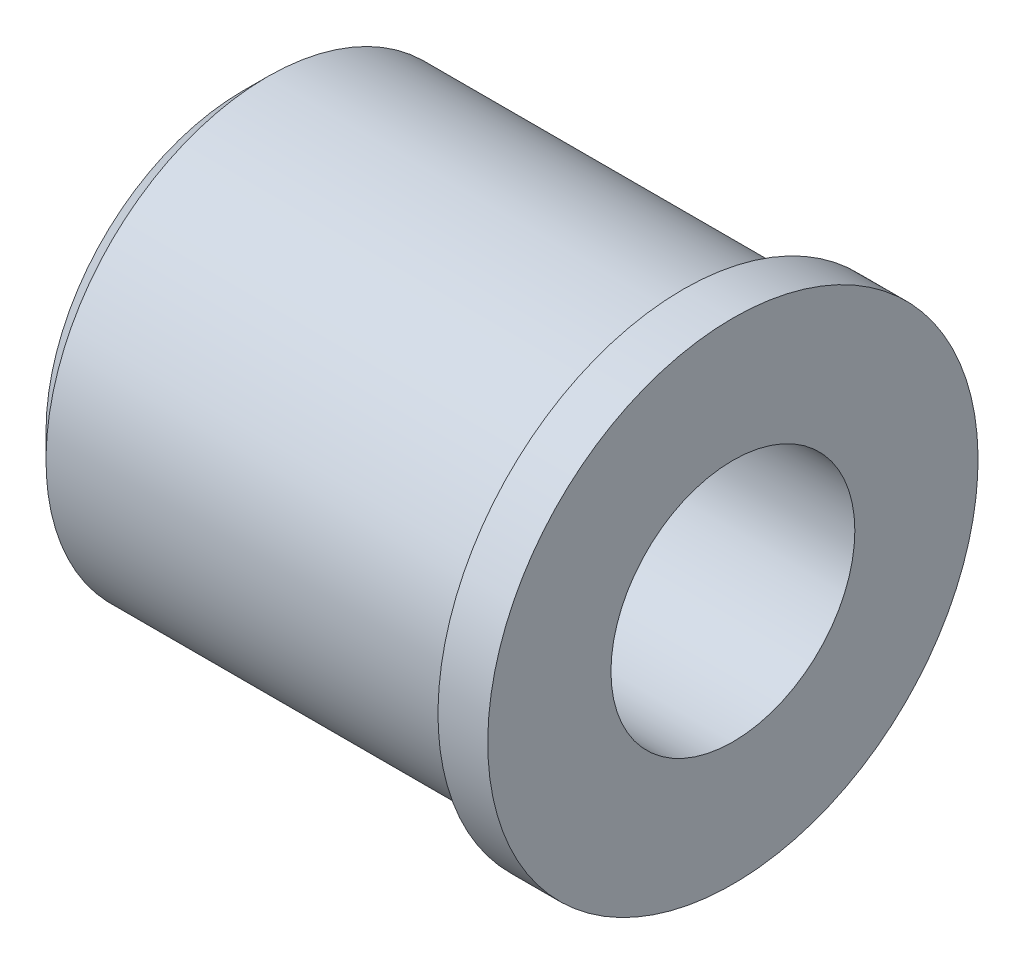
SolidWorks part; units mm, degrees
ref_plane "Front" through (0, 0, 0) normal (0, 0, 1) x (1, 0, 0)
ref_plane "Top" through (0, 0, 0) normal (0, 1, 0) x (1, 0, 0)
ref_plane "Right" through (0, 0, 0) normal (1, 0, 0) x (0, 0, -1)
sketch "Sketch1" plane through (0, 0, 0) normal (0, 0, 1) x (1, 0, 0)
  line L0 (0, 0) -> (-5.0038, 0) construction
  line L9 (0, 2.5019) -> (0, -2.5019)
  line L10 (-5.0038, 2.0066) -> (-5.0038, -2.0066)
  line L11 (-5.0038, 2.0066) -> (-4.7498, 2.2606)
  line L12 (-5.0038, -2.0066) -> (-4.7498, -2.2606)
  line L13 (-0.508, -2.2606) -> (-4.7498, -2.2606)
  line L14 (-0.508, 2.2606) -> (-4.7498, 2.2606)
  line L15 (-0.508, 2.5019) -> (0, 2.5019)
  line L16 (-0.508, 2.5019) -> (-0.508, -2.5019)
  line L17 (-0.508, -2.5019) -> (0, -2.5019)
revolve "Revolve1" add sketch "Sketch1" angle 360 about L0
hole_wizard "M3x0.25-4h Tapped Hole1" positions "3DSketch1" profile "Sketch3" tap size "M1.2x0.25" standard "Ansi Metric" end condition through all
sketch3d "3DSketch1"
  point P1 (0, 0, 0)
sketch "Sketch3" plane through (0, 0, 0) normal (0, 1, 0) x (0, 0, -1)
  line L0 (0, 0) -> (0, 5.0038)
  line L1 (0, 5.0038) -> (1.2446, 5.0038)
  line L2 (1.2446, 5.0038) -> (1.2446, 0)
  line L5 (1.2446, 0) -> (0, 0)
  line L11 (0, -6.35) -> (0, 107.95) construction
  dimension "Thru Tap Drill Dia." = 2.4892
  dimension "Thru Tap Drill Depth" = 5.0038
cosmetic thread "Hole Thread1" parameters "D2"=2.9972
